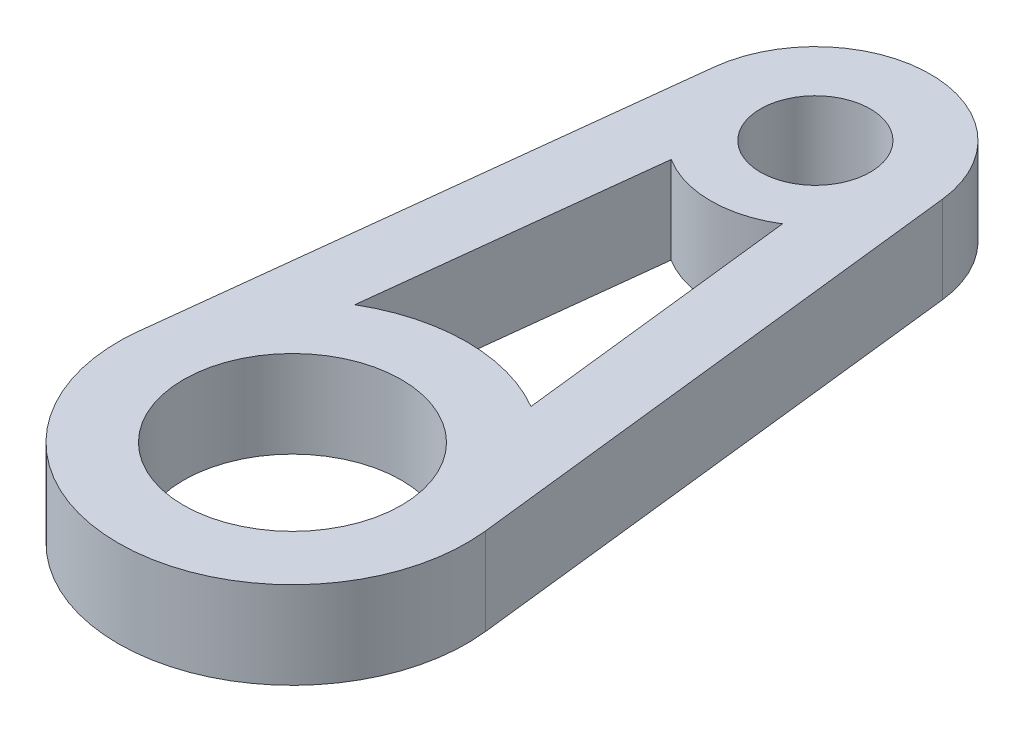
SolidWorks part; units mm, degrees
material "6061-T6 (SS)"
ref_plane "X-Y Datum" through (0, 0, 0) normal (0, 0, 1) x (1, 0, 0)
ref_plane "X-Z Datum" through (0, 0, 0) normal (0, 1, 0) x (1, 0, 0)
ref_plane "Y-Z Datum" through (0, 0, 0) normal (1, 0, 0) x (0, 0, -1)
sketch "Sketch2" plane through (0, 0, 0) normal (0, 1, 0) x (1, 0, 0)
  line L9 (4.164, 0.475) -> (6.3091, -18.3303)
  line L10 (-4.164, 0.475) -> (-6.3091, -18.3303)
  line L11 (0, -19.05) -> (0, 0) construction
  line L12 (3.2097, -13.5709) -> (2.0295, -3.2245)
  line L13 (-3.2097, -13.5709) -> (-2.0295, -3.2245)
  circle A0 centre (0, 0) radius 2
  arc A2 (-4.164, 0.475) -> (4.164, 0.475) centre (0, 0) cw
  circle A4 centre (0, -19.05) radius 3.9688
  arc A5 (6.3091, -18.3303) -> (-6.3091, -18.3303) centre (0, -19.05) cw
  arc A6 (2.0295, -3.2245) -> (-2.0295, -3.2245) centre (0, 0) cw
  arc A7 (3.2097, -13.5709) -> (-3.2097, -13.5709) centre (0, -19.05) ccw
  dimension "D3" = 6.35
  dimension "D1" = 4
  dimension "D5" = 7.9375
  dimension "D2" = 4.191
  dimension "D6" = 6.35
  dimension "D7" = 3.81
  dimension "D4" = 19.05
  dimension "D8" = 2.54
  dimension "D9" = 2.54
extrude "Boss-Extrude1" add sketch "Sketch2" along normal blind 3.175
